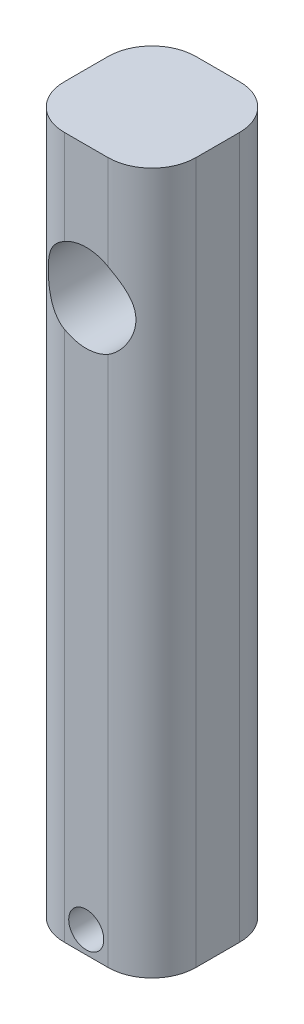
SolidWorks part; units mm, degrees
ref_plane "Front Plane" through (0, 0, 0) normal (0, 0, 1) x (1, 0, 0)
ref_plane "Top Plane" through (0, 0, 0) normal (0, 1, 0) x (1, 0, 0)
ref_plane "Right Plane" through (0, 0, 0) normal (1, 0, 0) x (0, 0, -1)
sketch "Sketch1" plane through (0, 0, 0) normal (0, 1, 0) x (1, 0, 0)
  line L1 (-6.35, -19.05) -> (6.35, -19.05)
  line L2 (-19.05, -6.35) -> (-19.05, 6.35)
  line L3 (-6.35, 19.05) -> (6.35, 19.05)
  line L4 (19.05, -6.35) -> (19.05, 6.35)
  line L5 (-19.05, -19.05) -> (19.05, 19.05) construction
  line L6 (-19.05, 19.05) -> (19.05, -19.05) construction
  arc A0 (-6.35, -19.05) -> (-19.05, -6.35) centre (-6.35, -6.35) cw
  arc A1 (6.35, -19.05) -> (19.05, -6.35) centre (6.35, -6.35) ccw
  arc A2 (6.35, 19.05) -> (19.05, 6.35) centre (6.35, 6.35) cw
  arc A3 (-19.05, 6.35) -> (-6.35, 19.05) centre (-6.35, 6.35) cw
  point P1 (0, 0)
  dimension "D3" = 12.7
  dimension "D1" = 38.1
  dimension "D2" = 38.1
extrude "Boss-Extrude2" add sketch "Sketch1" along normal blind 203.2
sketch "Sketch4" plane through (0, 0, 0) normal (0, 0, 1) x (1, 0, 0)
  line L0 (0, 203.2) -> (0, 0) construction
  line L1 (6.35, 203.2) -> (-6.35, 203.2) construction
  circle A0 centre (0, 164.846) radius 12.7
  circle A1 centre (0, 6.35) radius 5.08
  dimension "D1" = 10.16
  dimension "D2" = 25.4
  dimension "D3" = 158.496
  dimension "D4" = 6.35
  dimension "D5" = 38.354
extrude "Cut-Extrude1" cut sketch "Sketch4" against normal blind 92.964 and the other way blind 76.2
